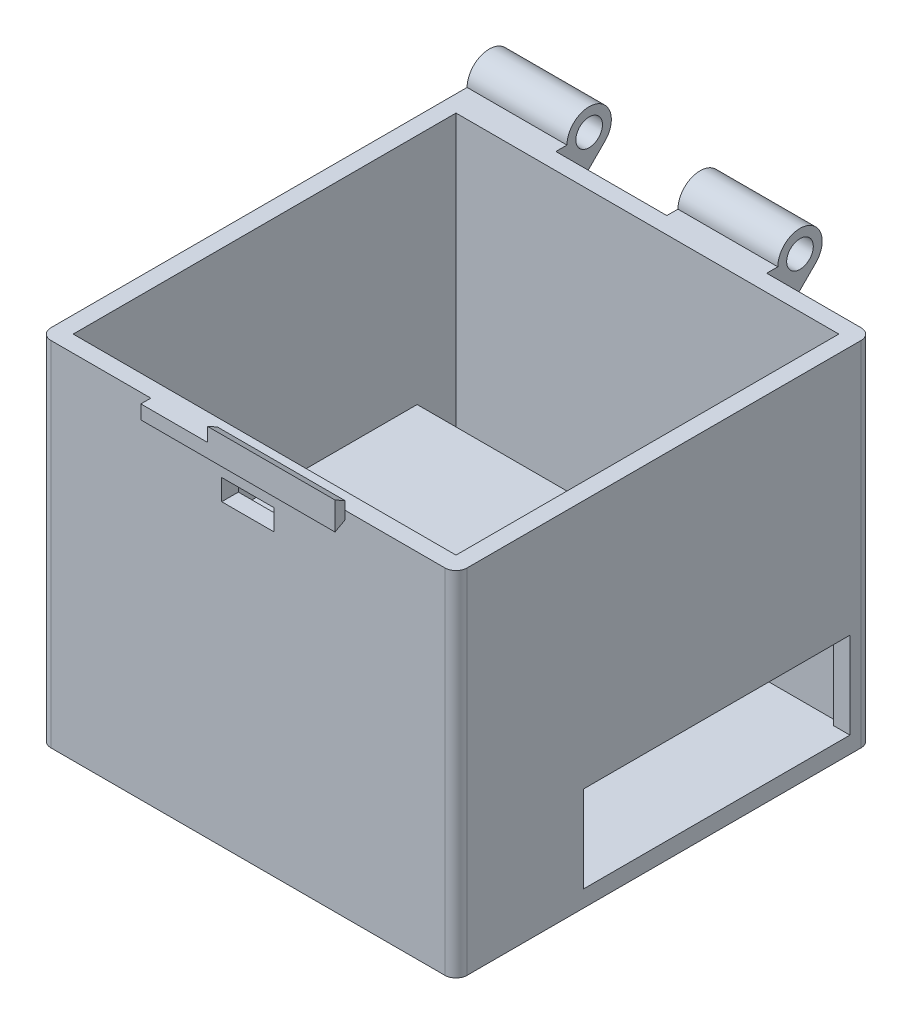
SolidWorks part; units mm, degrees
ref_plane "Front Plane" through (0, 0, 0) normal (0, 0, 1) x (1, 0, 0)
ref_plane "Top Plane" through (0, 0, 0) normal (0, 1, 0) x (1, 0, 0)
ref_plane "Right Plane" through (0, 0, 0) normal (1, 0, 0) x (0, 0, -1)
sketch "Sketch1" plane through (0, 0, 0) normal (0, 1, 0) x (1, 0, 0)
  line L1 (-47.625, 47.625) -> (47.625, 47.625)
  line L2 (-47.625, 47.625) -> (-47.625, -47.625)
  line L3 (-47.625, -47.625) -> (47.625, -47.625)
  line L4 (47.625, 47.625) -> (47.625, -47.625)
  point P4 (0, 47.625)
  point P6 (47.625, 0)
  dimension "D1" = 95.25
  dimension "D2" = 95.25
extrude "Boss-Extrude1" add sketch "Sketch1" along normal blind 57.15
shell "Shell1" thickness 3.81
sketch "Sketch2" plane through (-47.625, 0, 0) normal (-1, 0, 0) x (0, 0, 1)
  line L0 (-58.8371, 53.5579) -> (-47.625, 42.3458)
  line L1 (-47.625, 57.15) -> (-47.625, 0) construction
  line L2 (-47.625, 57.15) -> (-50.165, 57.15)
  arc A0 (-50.165, 57.15) -> (-58.8371, 53.5579) centre (-55.245, 57.15) ccw
  circle A1 centre (-55.245, 57.15) radius 3.048
  line M5 (-47.625, 57.15) -> (-47.625, 0)
  dimension "D1" = 7.62
  dimension "D2" = 45
  dimension "D3" = 10.16
  dimension "D4" = 6.096
extrude "Boss-Extrude2" add sketch "Sketch2" against normal blind 22.86 contours L2 A0 L0 A1 M5
sketch "Sketch5" plane through (47.625, 0, 0) normal (1, 0, 0) x (0, 0, -1)
  line L3 (50.165, 57.15) -> (47.625, 57.15)
  line L4 (47.625, 57.15) -> (47.625, 42.3458)
  line L5 (47.625, 42.3458) -> (58.8371, 53.5579)
  line L6 (50.165, 57.15) -> (47.625, 57.15)
  line L7 (47.625, 57.15) -> (47.625, 42.3458)
  line L8 (47.625, 42.3458) -> (58.8371, 53.5579)
  circle A1 centre (55.245, 57.15) radius 3.048
  circle A2 centre (55.245, 57.15) radius 3.048
  arc A3 (58.8371, 53.5579) -> (50.165, 57.15) centre (55.245, 57.15) ccw
  arc A4 (58.8371, 53.5579) -> (50.165, 57.15) centre (55.245, 57.15) ccw
  dimension "D1" = 0
  dimension "D2" = 0
extrude "Boss-Extrude3" add sketch "Sketch5" against normal blind 22.86 from offset 24.13 offset against normal yes
sketch "Sketch6" plane through (0, 0, 47.625) normal (0, 0, 1) x (1, 0, 0)
  line L0 (0, 57.15) -> (0, 0) construction
  line L1 (-47.625, 57.15) -> (47.625, 57.15) construction
  line L3 (-6, 49.53) -> (6, 49.53)
  line L4 (-6, 49.53) -> (-6, 44.73)
  line L5 (-6, 44.73) -> (6, 44.73)
  line L6 (6, 49.53) -> (6, 44.73)
  line L7 (-6, 49.53) -> (6, 44.73) construction
  line L8 (-6, 44.73) -> (6, 49.53) construction
  point P5 (0, 47.13)
  dimension "D1" = 4.8
  dimension "D2" = 12
  dimension "D3" = 7.62
extrude "Cut-Extrude1" cut sketch "Sketch6" against normal blind 3.81
sketch "Sketch8" plane through (0, 0, 0) normal (0, -1, 0) x (1, 0, 0)
  line L0 (47.625, -47.625) -> (-47.625, -47.625) construction
  line L1 (41.275, -42.545) -> (-42.545, -42.545)
  line L3 (41.275, 18.415) -> (-42.545, 18.415)
  line L4 (-42.545, -42.545) -> (-42.545, 18.415)
  line L5 (-47.625, -47.625) -> (-47.625, 47.625) construction
  line L6 (41.275, -42.545) -> (47.625, -42.545)
  line L7 (47.625, 47.625) -> (47.625, -47.625) construction
  line L8 (41.275, 18.415) -> (47.625, 18.415)
  line L9 (47.625, -47.625) -> (47.625, -42.545)
  line L13 (-47.625, 47.625) -> (-47.625, -47.625)
  line L14 (-47.625, -47.625) -> (47.625, -47.625)
  line L15 (47.625, -47.625) -> (47.625, 47.625)
  line L16 (47.625, 47.625) -> (-47.625, 47.625)
  line L17 (-47.625, 47.625) -> (-47.625, -47.625)
  line L18 (-47.625, -47.625) -> (47.625, -47.625)
  line L19 (47.625, 18.415) -> (47.625, 47.625)
  line L20 (47.625, 47.625) -> (-47.625, 47.625)
  dimension "D1" = 60.96
  dimension "D2" = 83.82
  dimension "D3" = 5.08
  dimension "D4" = 5.08
  dimension "D5" = 0
extrude "Boss-Extrude4" add sketch "Sketch8" along normal blind 19.812
sketch "Sketch9" plane through (47.625, 0, 0) normal (1, 0, 0) x (0, 0, -1)
  line L1 (-47.625, -19.812) -> (47.625, -19.812)
  line L2 (-47.625, -19.812) -> (-47.625, -23.622)
  line L3 (-47.625, -23.622) -> (47.625, -23.622)
  line L4 (47.625, -19.812) -> (47.625, -23.622)
  dimension "D1" = 3.81
extrude "Boss-Extrude5" add sketch "Sketch9" against normal through all
sketch "Sketch10" plane through (0, 3.81, 0) normal (0, 1, 0) x (1, 0, 0)
  line L0 (43.815, -43.815) -> (43.815, 43.815) construction
  line L1 (-43.815, 43.815) -> (43.815, 43.815)
  line L2 (-43.815, 43.815) -> (-43.815, 34.925)
  line L3 (-43.815, 34.925) -> (43.815, 34.925)
  line L4 (43.815, 43.815) -> (43.815, 34.925)
  dimension "D1" = 8.89
extrude "Cut-Extrude2" cut sketch "Sketch10" against normal up to surface (23.622 mm away) up to face at (2.54, -19.812, -12.065)
sketch "Sketch11" plane through (0, 3.81, 0) normal (0, 1, 0) x (1, 0, 0)
  line L0 (-43.815, 34.925) -> (-43.815, -43.815) construction
  line L1 (-43.815, -9.525) -> (43.815, -9.525)
  line L2 (-43.815, -9.525) -> (-43.815, -18.415)
  line L3 (-43.815, -18.415) -> (43.815, -18.415)
  line L4 (43.815, -9.525) -> (43.815, -18.415)
  line L5 (43.815, -43.815) -> (43.815, 43.815) construction
  line L8 (47.625, 47.625) -> (23.495, 47.625) construction
  dimension "D1" = 8.89
  dimension "D2" = 66.04
extrude "Cut-Extrude3" cut sketch "Sketch11" against normal up to surface (23.622 mm away) up to face at (1.27, -19.812, -25.7175)
fillet "Fillet1" radius 2.54 4 edges at (47.625, 16.764, -47.625) (-47.625, 9.3619, -47.625) (-47.625, 16.764, 47.625) (47.625, 16.764, 47.625)
sketch "Sketch12" plane through (47.625, 0, 0) normal (1, 0, 0) x (0, 0, -1)
  line L0 (-47.625, 44.73) -> (-47.625, 49.53) construction
  line L2 (-47.625, 55.245) -> (-47.625, 59.055)
  line L4 (-49.911, 53.975) -> (-49.911, 60.325)
  line L5 (-45.085, 57.15) -> (-47.625, 57.15) construction
  line L6 (-49.911, 60.325) -> (-47.625, 59.055)
  line L7 (-47.625, 55.245) -> (-49.911, 53.975)
  point P6 (-47.625, 57.15)
  point P9 (-47.625, 59.055)
  point P10 (-47.625, 55.245)
  dimension "D1" = 6.35
  dimension "D2" = 1.27
  dimension "D3" = 1.27
  dimension "D4" = 2.286
extrude "Boss-Extrude6" add sketch "Sketch12" against normal mid plane 44.45 from offset 47.625 offset against normal yes
sketch "Sketch13" plane through (0, 0, 49.911) normal (0, 0, 1) x (1, 0, 0)
  line L1 (-6.985, 57.15) -> (-6.985, 60.325)
  line L3 (-22.225, 57.15) -> (-6.985, 57.15)
  dimension "D1" = 15.24
extrude "Cut-Extrude4" cut sketch "Sketch13" against normal blind 3.81 and the other way through all
